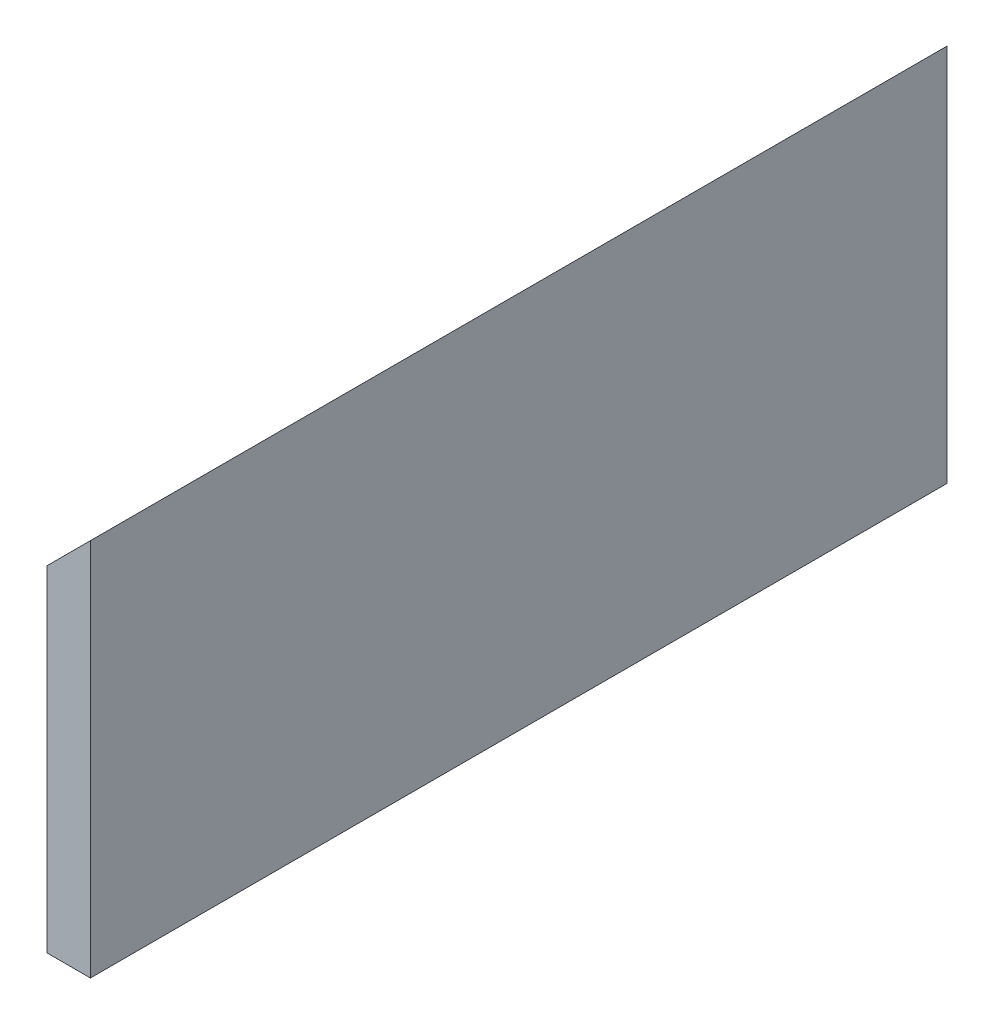
SolidWorks part; units mm, degrees
ref_plane "Plan de face" through (0, 0, 0) normal (0, 0, 1) x (1, 0, 0)
ref_plane "Plan de dessus" through (0, 0, 0) normal (0, 1, 0) x (1, 0, 0)
ref_plane "Plan de droite" through (0, 0, 0) normal (1, 0, 0) x (0, 0, -1)
sketch "Esquisse1" plane through (0, 0, 0) normal (0, 0, 1) x (1, 0, 0)
  line L2 (-300, 185.3139) -> (-300, 52.6889)
  line L3 (-300, 52.6889) -> (-315.25, 52.6889)
  line L4 (-315.25, 170.0639) -> (-315.25, 52.6889)
  line L7 (-315.25, 170.0639) -> (-300, 185.3139)
  line L10 (0, 60.3139) -> (-299, 60.3139) construction
  dimension "D1" = 7.625
extrude "Boss.-Extru.1" add sketch "Esquisse1" along normal up to surface (300 mm away)
